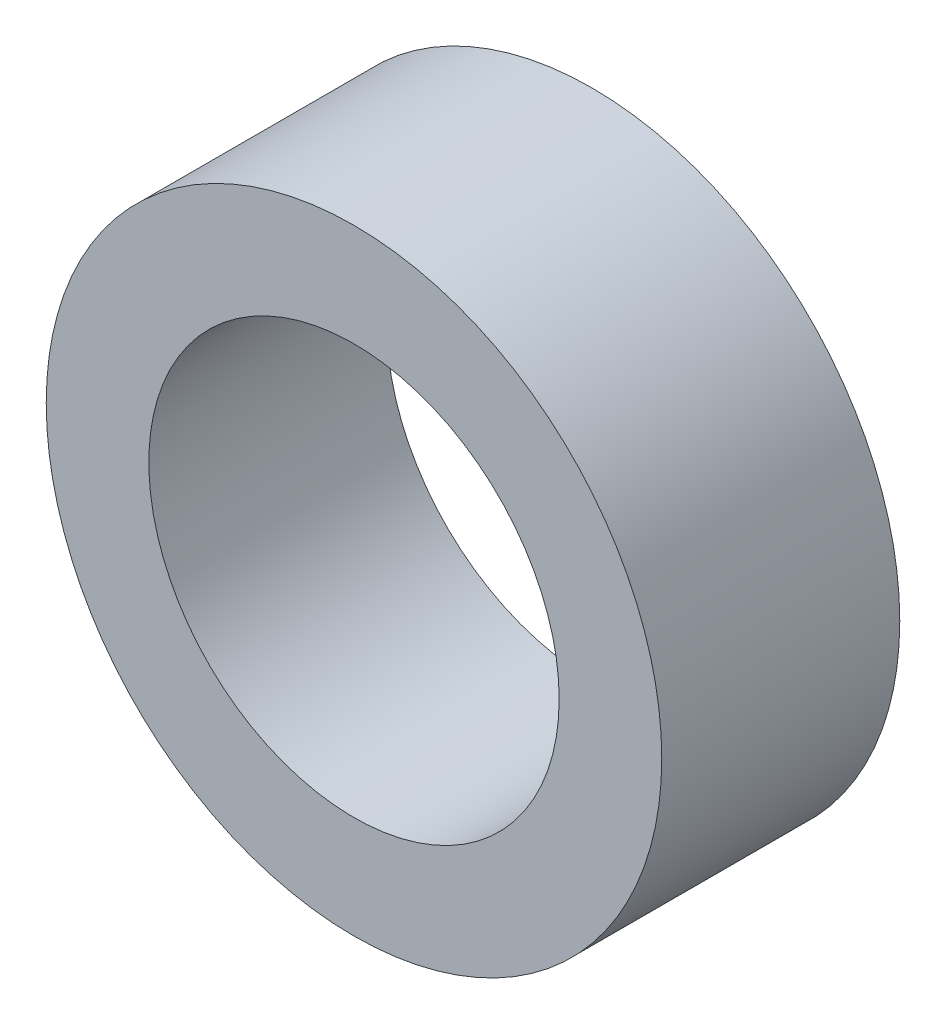
SolidWorks part; units mm, degrees
ref_plane "Front" through (0, 0, 0) normal (0, 0, 1) x (1, 0, 0)
ref_plane "Top" through (0, 0, 0) normal (0, 1, 0) x (1, 0, 0)
ref_plane "Right" through (0, 0, 0) normal (1, 0, 0) x (0, 0, -1)
sketch "Sketch1" plane through (0, 0, 0) normal (0, 0, 1) x (1, 0, 0)
  circle A0 centre (0, 0) radius 9.525
  circle A1 centre (0, 0) radius 6.35
  dimension "D1" = 3.175
  dimension "D2" = 12.7
extrude "Boss-Extrude1" add sketch "Sketch1" along normal blind 7.366
